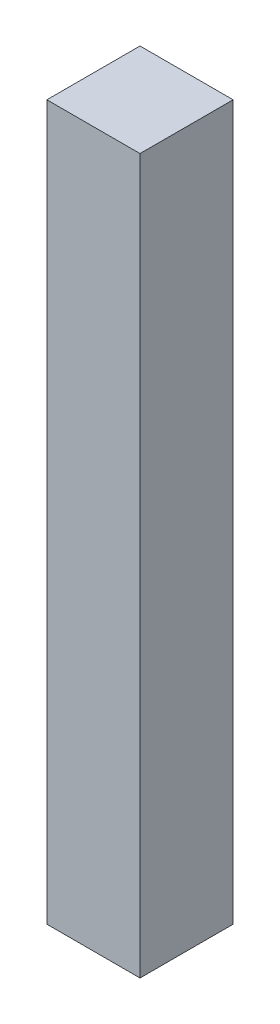
SolidWorks part; units mm, degrees
ref_plane "Front Plane" through (0, 0, 0) normal (0, 0, 1) x (1, 0, 0)
ref_plane "Top Plane" through (0, 0, 0) normal (0, 1, 0) x (1, 0, 0)
ref_plane "Right Plane" through (0, 0, 0) normal (1, 0, 0) x (0, 0, -1)
sketch "Sketch1" plane through (0, 0, 0) normal (0, 1, 0) x (1, 0, 0)
  line L1 (-15, -15) -> (15, -15)
  line L2 (-15, -15) -> (-15, 15)
  line L3 (-15, 15) -> (15, 15)
  line L4 (15, -15) -> (15, 15)
  line L5 (-15, -15) -> (15, 15) construction
  line L6 (-15, 15) -> (15, -15) construction
  point P0 (0, 0)
  dimension "D1" = 30
  dimension "D2" = 30
extrude "Boss-Extrude1" add sketch "Sketch1" along normal mid plane 230
